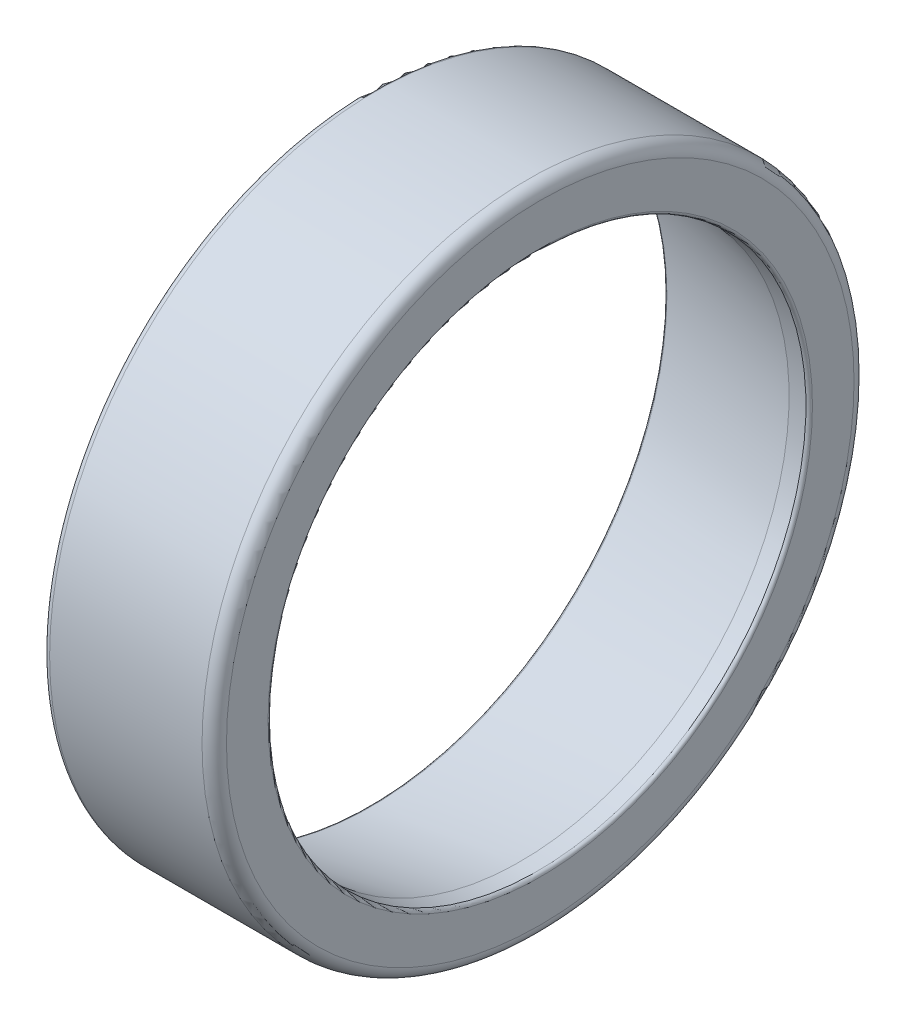
SolidWorks part; units mm, degrees
ref_plane "Front Plane" through (0, 0, 0) normal (0, 0, 1) x (1, 0, 0)
ref_plane "Top Plane" through (0, 0, 0) normal (0, 1, 0) x (1, 0, 0)
ref_plane "Right Plane" through (0, 0, 0) normal (1, 0, 0) x (0, 0, -1)
sketch "Sketch1" plane through (0, 0, 0) normal (0, 0, 1) x (1, 0, 0)
  line L0 (0, 0) -> (21, 0) construction
  line L1 (3.4, 37.5505) -> (3.4, 25.3856) construction
  line L2 (0, 37.5505) -> (3.4, 37.5505) construction
  line L3 (0, 37.5505) -> (0, 27.5) construction
  line L4 (0, 27.5) -> (21, 27.5) construction
  line L5 (21, 24.077) -> (21, 27.5) construction
  line L6 (2.0778, 34.0468) -> (20.2251, 30.8469) construction
  line L7 (22, 33) -> (22, 40)
  line L8 (22, 40) -> (1, 40)
  line L9 (1, 36.2677) -> (1, 40)
  line L10 (3.4, 25.3856) -> (18.3572, 24.077) construction
  line L11 (1, 36.2677) -> (19.5319, 33)
  line L12 (4.0729, 30.4964) -> (18.9445, 28.5385) construction
  line L13 (3.4, 25.3856) -> (4.7457, 35.6072) construction
  line L14 (18.3572, 24.077) -> (19.5319, 33) construction
  line L15 (18.3572, 24.077) -> (21, 24.077) construction
  line L16 (23.2, 27.3016) -> (23.2, 25.077) construction
  line L17 (1.8, 32.4711) -> (19.9473, 29.2712) construction
  line L18 (21.6, 27.3016) -> (21.6, 25.077) construction
  line L19 (21.6, 25.077) -> (23.2, 25.077) construction
  line L20 (1.8, 32.4711) -> (2.0778, 34.0468) construction
  line L21 (19.5319, 33) -> (22, 33)
  arc A0 (19.9473, 29.2712) -> (21.6, 27.3016) centre (19.6, 27.3016) cw construction
  arc A1 (20.2251, 30.8469) -> (23.2, 27.3016) centre (19.6, 27.3016) cw construction
  dimension "D14" = 2
  dimension "D15" = 3.6
  dimension "D1" = 21
  dimension "D2" = 27.5
  dimension "D3" = 40
  dimension "D4" = 1
  dimension "D5" = 21
  dimension "D6" = 5
  dimension "D7" = 1.8
  dimension "D8" = 2.5
  dimension "D9" = 15
  dimension "D10" = 9
  dimension "D11" = 2
  dimension "D12" = 1.6
  dimension "D13" = 1.6
  dimension "D16" = 0.6
  dimension "D17" = 1
  dimension "D18" = 3.4
  dimension "D19" = 5
  dimension "D20" = 7
  dimension "D21" = 30.8469
  dimension "D22" = 40
revolve "Revolve1" add sketch "Sketch1" angle 360 about L0
fillet "Fillet1" radius 1.5 1 edges at (22, 0, 40)
fillet "Fillet2" radius 0.8 1 edges at (1, 0, 40)
fillet "Fillet3" radius 0.4 2 edges at (1, 0, 36.2677) (22, 0, 33)
